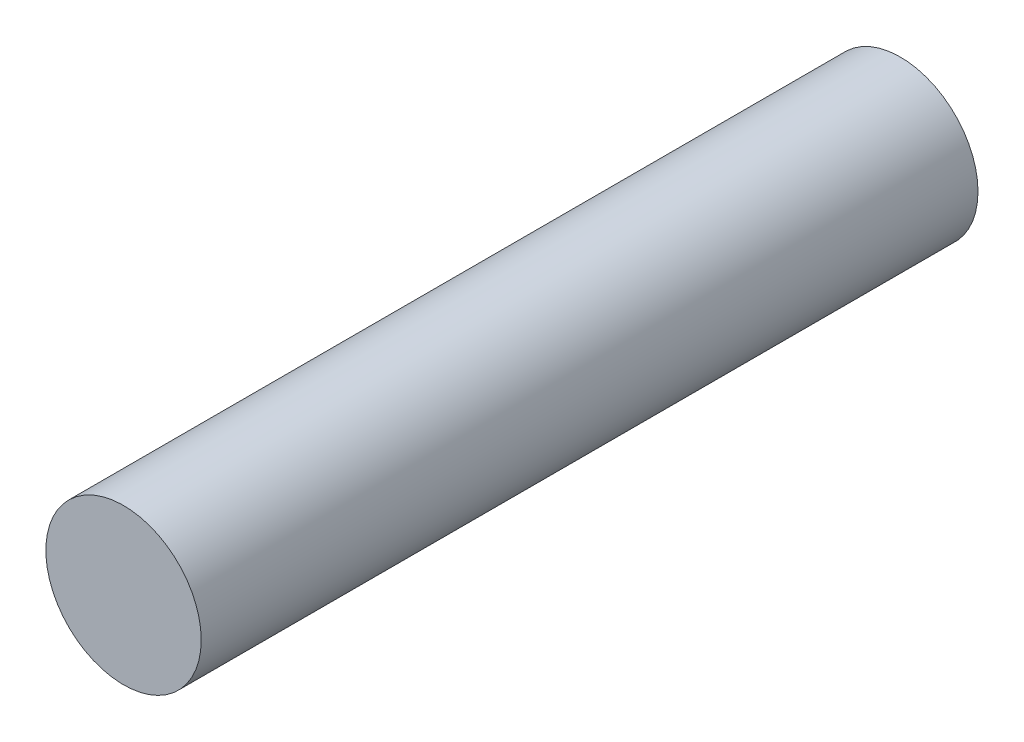
SolidWorks part; units mm, degrees
material "AISI 1020"
ref_plane "Front Plane" through (0, 0, 0) normal (0, 0, 1) x (1, 0, 0)
ref_plane "Top Plane" through (0, 0, 0) normal (0, 1, 0) x (1, 0, 0)
ref_plane "Right Plane" through (0, 0, 0) normal (1, 0, 0) x (0, 0, -1)
sketch "Sketch1" plane through (0, 0, 0) normal (0, 0, 1) x (1, 0, 0)
  circle A0 centre (0, 0) radius 3.175
  dimension "D1" = 6.35
extrude "Boss-Extrude1" add sketch "Sketch1" along normal blind 31.75
